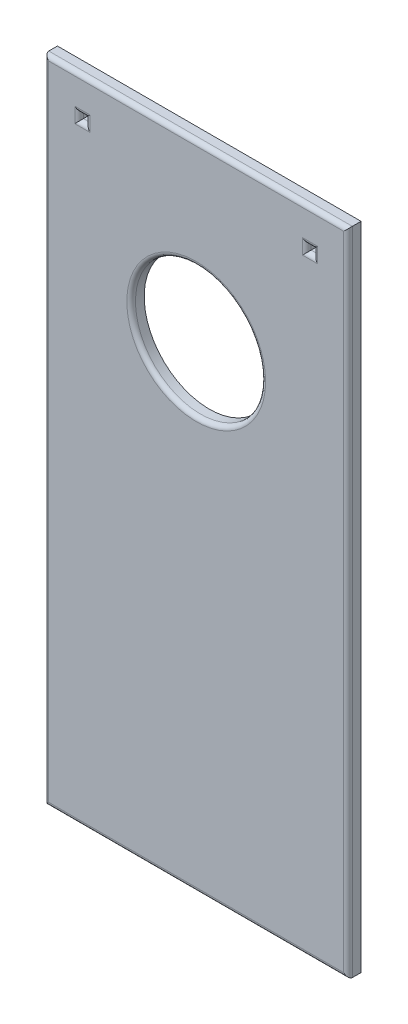
SolidWorks part; units mm, degrees
material "PBT General Purpose"
ref_plane "Front Plane" through (0, 0, 0) normal (0, 0, 1) x (1, 0, 0)
ref_plane "Top Plane" through (0, 0, 0) normal (0, 1, 0) x (1, 0, 0)
ref_plane "Right Plane" through (0, 0, 0) normal (1, 0, 0) x (0, 0, -1)
sketch "Sketch1" plane through (0, 0, 0) normal (0, 0, 1) x (1, 0, 0)
  line L0 (0, 20) -> (0, -20) construction
  line L1 (-35, 20) -> (35, 20)
  line L2 (-35, 20) -> (-35, -130)
  line L3 (-35, -130) -> (35, -130)
  line L4 (35, 20) -> (35, -130)
  dimension "D1" = 70
  dimension "D2" = 150
  dimension "D3" = 40
extrude "Extrude1" add sketch "Sketch1" along normal blind 3
sketch "Sketch2" plane through (0, 0, 3) normal (0, 0, 1) x (1, 0, 0)
  line L1 (35, 20) -> (-35, 20) construction
  line L2 (0, 0) -> (0, -20) construction
  circle A0 centre (0, -20) radius 15
  dimension "D1" = 30
  dimension "D2" = 40
extrude "Extrude2" cut sketch "Sketch2" against normal up to next
sketch "Sketch4" plane through (0, 0, 3) normal (0, 0, 1) x (1, 0, 0)
  line L0 (35, 20) -> (-35, 20) construction
  line L1 (-27, 12) -> (-25.5, 12)
  line L2 (-27, 12) -> (-27, 10.5)
  line L3 (-27, 10.5) -> (-25.5, 10.5)
  line L4 (-25.5, 12) -> (-25.5, 10.5)
  line L5 (25.5, 12) -> (27, 12)
  line L6 (25.5, 12) -> (25.5, 10.5)
  line L7 (25.5, 10.5) -> (27, 10.5)
  line L8 (27, 12) -> (27, 10.5)
  line L9 (-25.5, 12) -> (25.5, 12) construction
  line L10 (-35, 20) -> (-35, -130) construction
  line L11 (35, -130) -> (35, 20) construction
  dimension "D1" = 8
  dimension "D2" = 8
  dimension "D3" = 1.5
  dimension "D4" = 8
extrude "Extrude3" cut sketch "Sketch4" against normal up to next
fillet "Fillet1" radius 1 13 edges at (0, 20, 3) (35, -55, 3) (0, -130, 3) (-35, -55, 3) (15, -20, 3) (-26.25, 10.5, 3) (-25.5, 11.25, 3) (-26.25, 12, 3) (-27, 11.25, 3) (26.25, 10.5, 3) (27, 11.25, 3) (26.25, 12, 3) (25.5, 11.25, 3)
